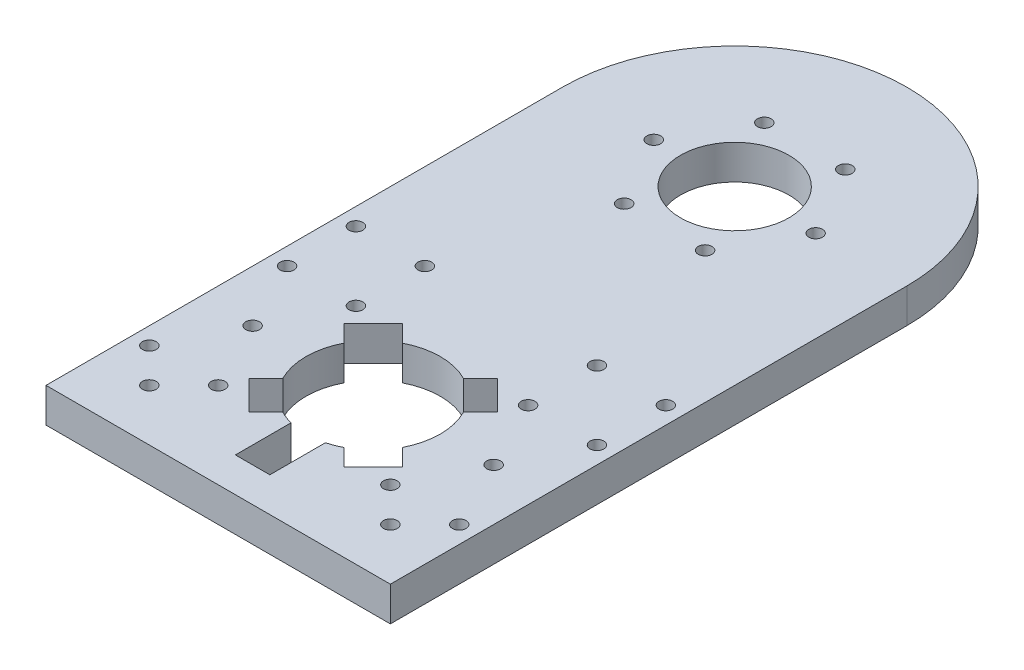
SolidWorks part; units mm, degrees
material "Acrylic (Medium-high impact)"
ref_plane "Front Plane" through (0, 0, 0) normal (0, 0, 1) x (1, 0, 0)
ref_plane "Top Plane" through (0, 0, 0) normal (0, 1, 0) x (1, 0, 0)
ref_plane "Right Plane" through (0, 0, 0) normal (1, 0, 0) x (0, 0, -1)
sketch "Sketch1" plane through (0, 0, 0) normal (0, 1, 0) x (1, 0, 0)
  line L0 (-2.3264, 11.6598) -> (-2.3264, -10.986) construction
  line L1 (-25.8407, 8.1193) -> (-12.3264, 8.1193) construction
  line L2 (-2.3264, 11.6598) -> (-2.3264, -10.986)
  line L3 (-52.3264, -141.8807) -> (47.6736, -141.8807)
  line L4 (47.6736, -141.8807) -> (47.6736, 8.1193)
  line L5 (-2.3264, 8.1193) -> (25.1292, 8.1193) construction
  line L6 (-52.3264, -141.8807) -> (-52.3264, 8.1193)
  arc A0 (47.6736, 8.1193) -> (-52.3264, 8.1193) centre (-2.3264, 8.1193) ccw
  circle A1 centre (-2.3264, 8.1193) radius 15.75
  circle A2 centre (-2.3264, 8.1193) radius 23.5 construction
  circle A3 centre (21.1736, 8.1193) radius 2
  circle A4 centre (9.4236, -12.2323) radius 2
  circle A5 centre (-14.0764, -12.2323) radius 2
  circle A6 centre (-25.8264, 8.1193) radius 2
  circle A7 centre (-14.0764, 28.4709) radius 2
  circle A8 centre (9.4236, 28.4709) radius 2
  circle A9 centre (-47.3264, -116.8807) radius 2
  circle A10 centre (42.6736, -116.8807) radius 2
  circle A11 centre (-37.3264, -126.8807) radius 2
  circle A12 centre (-37.3264, -96.8807) radius 2
  circle A13 centre (-47.3264, -76.8807) radius 2
  circle A14 centre (42.6736, -76.8807) radius 2
  circle A15 centre (-47.3264, -56.8807) radius 2
  circle A16 centre (42.6736, -56.8807) radius 2
  circle A17 centre (-27.3264, -116.8807) radius 2
  circle A18 centre (22.6736, -116.8807) radius 2
  circle A19 centre (-27.3264, -56.8807) radius 2
  circle A20 centre (-27.3264, -76.8807) radius 2
  circle A21 centre (22.6736, -56.8807) radius 2
  circle A22 centre (22.6736, -76.8807) radius 2
  circle A23 centre (32.6736, -96.8807) radius 2
  circle A24 centre (32.6736, -126.8807) radius 2
  point P26 (-2.3264, 8.1193)
  dimension "D1" = 100
  dimension "D3" = 31.5
  dimension "D4" = 47
  dimension "D5" = 4
  dimension "D7" = 4
  dimension "D8" = 4
  dimension "D9" = 4
  dimension "D10" = 4
  dimension "D11" = 4
  dimension "D12" = 4
  dimension "D13" = 4
  dimension "D14" = 4
  dimension "D20" = 4
  dimension "D21" = 4
  dimension "D22" = 4
  dimension "D23" = 4
  dimension "D24" = 4
  dimension "D25" = 4
  dimension "D28" = 4
  dimension "D54" = 4
  dimension "D2" = 150
  dimension "D6" = 6
  dimension "D15" = 25
  dimension "D16" = 5
  dimension "D17" = 25
  dimension "D18" = 5
  dimension "D19" = 15
  dimension "D26" = 25
  dimension "D27" = 20
  dimension "D29" = 20
  dimension "D30" = 25
  dimension "D31" = 15
  dimension "D32" = 45
  dimension "D33" = 15
  dimension "D34" = 15
  dimension "D35" = 15
  dimension "D36" = 15
  dimension "D37" = 45
  dimension "D38" = 5
  dimension "D39" = 5
  dimension "D40" = 5
  dimension "D41" = 5
  dimension "D42" = 85
  dimension "D43" = 85
  dimension "D44" = 20
  dimension "D45" = 20
  dimension "D46" = 20
  dimension "D47" = 20
  dimension "D48" = 85
  dimension "D49" = 20
  dimension "D50" = 20
  dimension "D51" = 20
  dimension "D52" = 20
  dimension "D53" = 85
extrude "Boss-Extrude3" add sketch "Sketch1" along normal blind 10
sketch "Sketch2" plane through (0, 10, 0) normal (0, 1, 0) x (1, 0, 0)
  line L0 (-52.3264, -141.8807) -> (-52.3264, 8.1193) construction
  line L2 (-52.3264, -141.8807) -> (47.6736, -141.8807) construction
  circle A0 centre (-2.3264, -96.8807) radius 19.5
  point P6 (-52.3264, -66.8807)
  dimension "D1" = 39
  dimension "D2" = 50
  dimension "D3" = 45
extrude "Cut-Extrude1" cut sketch "Sketch2" against normal blind 10
sketch "Sketch3" plane through (0, 10, 0) normal (0, 1, 0) x (1, 0, 0)
  line L0 (-7.3264, -131.8807) -> (-7.3264, -115.7288)
  line L1 (-52.3264, -141.8807) -> (47.6736, -141.8807) construction
  line L2 (2.6736, -131.8807) -> (2.6736, -115.7288)
  line L3 (-52.3264, -141.8807) -> (-52.3264, 8.1193) construction
  line L4 (-7.3264, -131.8807) -> (2.6736, -131.8807)
  circle A0 centre (-2.3264, -96.8807) radius 19.5 construction
  arc A1 (-7.3264, -115.7288) -> (2.6736, -115.7288) centre (-2.3264, -96.8807) ccw
  dimension "D1" = 10
  dimension "D2" = 45
  dimension "D3" = 10
extrude "Cut-Extrude2" cut sketch "Sketch3" against normal blind 10
sketch "Sketch4" plane through (0, 10, 0) normal (0, 1, 0) x (1, 0, 0)
  line L0 (-2.3264, -96.8807) -> (-2.3264, -84.8807) construction
  line L1 (6.5506, -79.5184) -> (11.4622, -74.6068)
  line L2 (11.4622, -74.6068) -> (19.9475, -83.0921)
  line L3 (15.0359, -88.0037) -> (19.9475, -83.0921)
  line L12 (15.0359, -105.7577) -> (19.9475, -110.6693)
  line L13 (19.9475, -110.6693) -> (11.4622, -119.1545)
  line L14 (6.5506, -114.243) -> (11.4622, -119.1545)
  line L18 (-11.2034, -114.243) -> (-16.115, -119.1545)
  line L19 (-16.115, -119.1545) -> (-24.6003, -110.6693)
  line L20 (-19.6887, -105.7577) -> (-24.6003, -110.6693)
  line L24 (-19.6887, -88.0037) -> (-24.6003, -83.0921)
  line L25 (-24.6003, -83.0921) -> (-16.115, -74.6068)
  line L26 (-11.2034, -79.5184) -> (-16.115, -74.6068)
  arc A0 (2.6736, -115.7288) -> (-7.3264, -115.7288) centre (-2.3264, -96.8807) ccw construction
  arc A1 (2.6736, -115.7288) -> (-1.3168, -77.4068) centre (-2.3264, -96.8807) ccw
  arc A2 (2.6736, -115.7288) -> (-7.3264, -115.7288) centre (-2.3264, -96.8807) ccw
  point P2 (-2.3264, -77.3807)
  point P42 (-2.3264, -96.8807)
  arc M29 (-7.3264, -115.7288) -> (2.6736, -115.7288) centre (-2.3264, -96.8807) cw
extrude "Cut-Extrude3" cut sketch "Sketch4" against normal blind 10 contours L26 L25 L24 M29 | L3 L2 L1 M29 | L14 L13 L12 M29 | L20 L19 L18 M29
